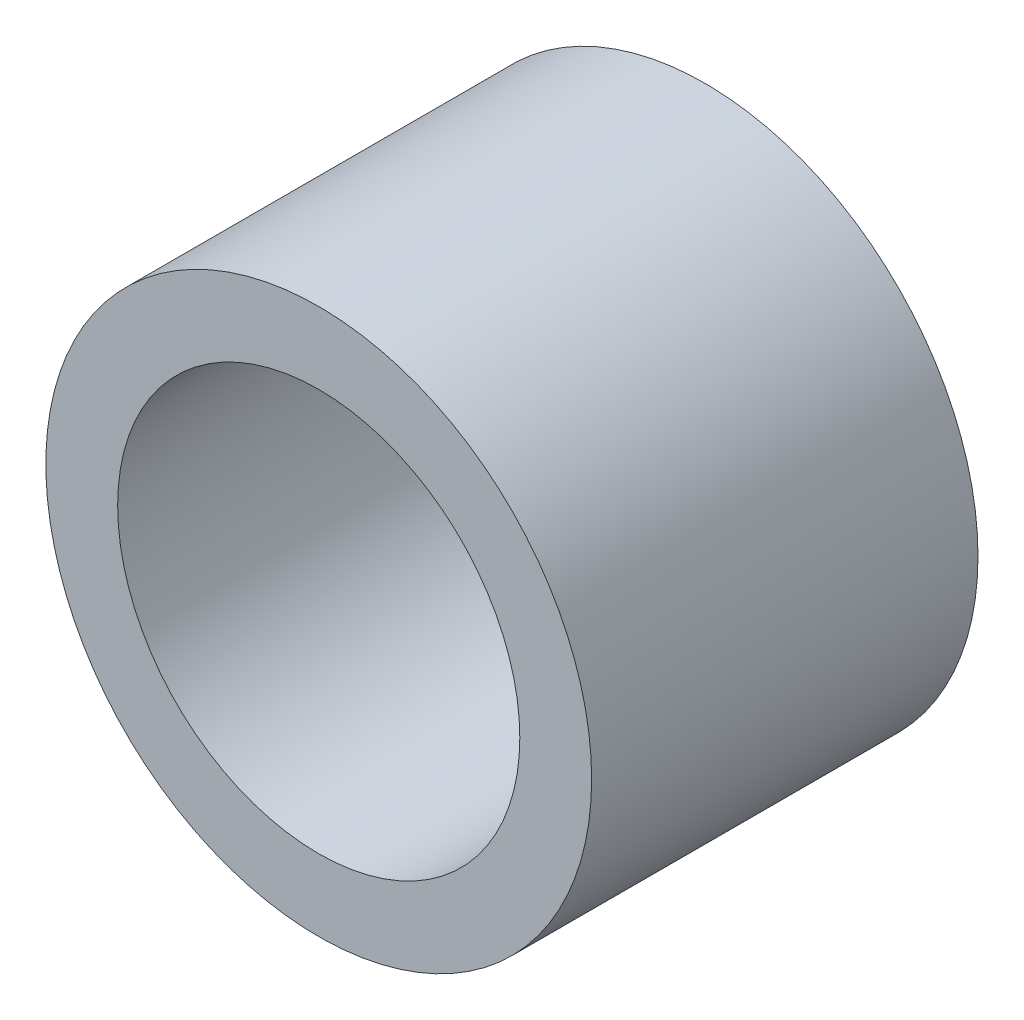
SolidWorks part; units mm, degrees
ref_plane "Front Plane" through (0, 0, 0) normal (0, 0, 1) x (1, 0, 0)
ref_plane "Top Plane" through (0, 0, 0) normal (0, 1, 0) x (1, 0, 0)
ref_plane "Right Plane" through (0, 0, 0) normal (1, 0, 0) x (0, 0, -1)
sketch "Sketch1" plane through (0, 0, 0) normal (0, 0, 1) x (1, 0, 0)
  circle A0 centre (0, 0) radius 4.826
  circle A1 centre (0, 0) radius 3.556
  dimension "D1" = 7.112
  dimension "D2" = 1.27
extrude "Boss-Extrude1" add sketch "Sketch1" along normal blind 6.8326
